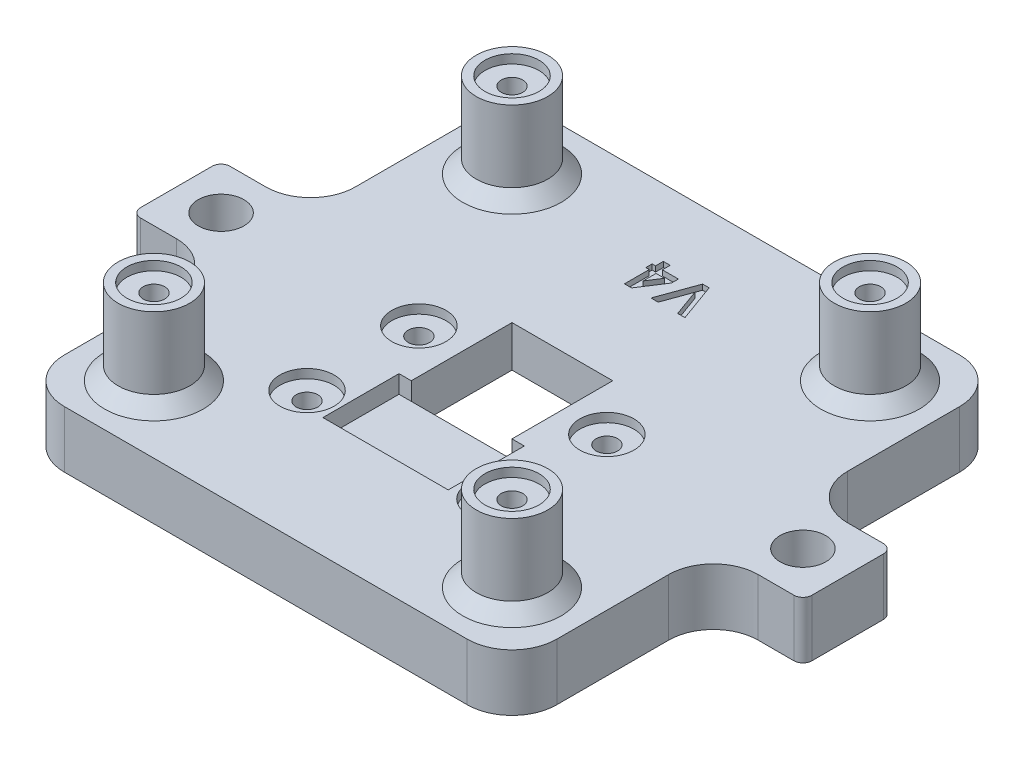
SolidWorks part; units mm, degrees
ref_plane "Front Plane" through (0, 0, 0) normal (0, 0, 1) x (1, 0, 0)
ref_plane "Top Plane" through (0, 0, 0) normal (0, 1, 0) x (1, 0, 0)
ref_plane "Right Plane" through (0, 0, 0) normal (1, 0, 0) x (0, 0, -1)
sketch "Sketch1" plane through (0, 0, 0) normal (0, 1, 0) x (1, 0, 0)
  line L1 (-27.5, 27.5) -> (27.5, 27.5)
  line L2 (-27.5, 27.5) -> (-27.5, -27.5)
  line L3 (-27.5, -27.5) -> (27.5, -27.5)
  line L4 (27.5, 27.5) -> (27.5, -27.5)
  line L5 (-27.5, 27.5) -> (27.5, -27.5) construction
  line L6 (-27.5, -27.5) -> (27.5, 27.5) construction
  point P0 (0, 0)
  dimension "D1" = 55
  dimension "D2" = 55
extrude "Boss-Extrude1" add sketch "Sketch1" along normal blind 6.35
sketch "Sketch2" plane through (0, 6.35, 0) normal (0, 1, 0) x (1, 0, 0)
  line L1 (-5.625, -5.625) -> (5.625, -5.625)
  line L2 (-5.625, -5.625) -> (-5.625, 5.625)
  line L3 (-5.625, 5.625) -> (5.625, 5.625)
  line L4 (5.625, -5.625) -> (5.625, 5.625)
  line L5 (-5.625, -5.625) -> (5.625, 5.625) construction
  line L6 (-5.625, 5.625) -> (5.625, -5.625) construction
  point P0 (0, 0)
  dimension "D1" = 11.25
extrude "Cut-Extrude1" cut sketch "Sketch2" against normal through all
sketch "Sketch3" plane through (0, 6.35, 0) normal (0, 1, 0) x (1, 0, 0)
  line L0 (0, 0) -> (0, 2.7158) construction
  line L1 (-7, -5.625) -> (7, -5.625)
  line L2 (-7, -5.625) -> (-7, -14.125)
  line L3 (-7, -14.125) -> (7, -14.125)
  line L4 (7, -5.625) -> (7, -14.125)
  line L6 (-5.625, -5.625) -> (5.625, -5.625) construction
  point P5 (0, -5.625)
  dimension "D1" = 14
  dimension "D2" = 8.5
extrude "Cut-Extrude2" cut sketch "Sketch3" against normal blind 2
sketch "Sketch4" plane through (0, 0, 0) normal (0, 1, 0) x (1, 0, 0)
  line L0 (0, 0) -> (0, 9.1234) construction
  line L2 (-12.5, 9.462) -> (12.5, 9.462) construction
  line L3 (-12.5, 9.462) -> (-12.5, -14.4) construction
  line L4 (-12.5, -14.4) -> (12.5, -14.4) construction
  line L5 (12.5, 9.462) -> (12.5, -14.4) construction
  point P7 (0, 9.462)
  point P8 (10.5, -12.4)
  point P9 (-10.5, -12.4)
  point P10 (-10.5, 0.1)
  point P11 (10.5, 0.1)
  dimension "D1" = 14.4
  dimension "D2" = 23.862
  dimension "D3" = 25
  dimension "D4" = 2
  dimension "D5" = 2
  dimension "D6" = 14.5
hole_wizard "CBORE for M2 SHCS2" positions "Sketch4" profile "Sketch15" counterbore size "M2" standard "ANSI Metric" end condition up to next
sketch "Sketch15" plane through (10.5, 0, -0.1) normal (1, 0, 0) x (0, 0, -1)
  line L0 (0, 0) -> (0, 6.35)
  line L1 (0, 6.35) -> (1.2, 6.35)
  line L3 (1.2, 6.35) -> (1.2, 2)
  line L4 (1.2, 2) -> (2.2, 2)
  line L5 (2.2, 2) -> (2.2, 0)
  line L7 (2.2, 0) -> (0, 0)
  line L11 (0, -6.35) -> (0, 107.95) construction
  dimension "Thru Hole Dia." = 2.4
  dimension "Thru Hole Depth" = 6.35
  dimension "C'Bore Dia." = 4.4
  dimension "C'Bore Depth" = 2
sketch "Sketch6" plane through (0, 6.35, 0) normal (0, 1, 0) x (1, 0, 0)
  line L1 (-20, -20) -> (20, -20) construction
  line L2 (-20, -20) -> (-20, 20) construction
  line L3 (-20, 20) -> (20, 20) construction
  line L4 (20, -20) -> (20, 20) construction
  line L5 (-20, -20) -> (20, 20) construction
  line L6 (-20, 20) -> (20, -20) construction
  circle A0 centre (-20, 20) radius 4
  circle A1 centre (20, 20) radius 4
  circle A2 centre (20, -20) radius 4
  circle A3 centre (-20, -20) radius 4
  point P0 (0, 0)
  dimension "D2" = 8
  dimension "D1" = 40
extrude "Boss-Extrude2" add sketch "Sketch6" along normal blind 9.5
sketch "Sketch10" plane through (0, 0, 0) normal (0, -1, 0) x (1, 0, 0)
  circle A0 centre (20, 20) radius 4 construction
  circle A1 centre (20, -20) radius 4 construction
  circle A2 centre (-20, -20) radius 4 construction
  circle A3 centre (-20, 20) radius 4 construction
  circle A4 centre (20, 20) radius 4 construction
  circle A5 centre (20, -20) radius 4 construction
  circle A6 centre (-20, -20) radius 4 construction
  circle A7 centre (-20, 20) radius 4 construction
  point P13 (-20, 20)
  point P14 (20, 20)
  point P15 (20, -20)
  point P16 (-20, -20)
hole_wizard "CBORE for M2 SHCS1" positions "Sketch10" profile "Sketch11" counterbore size "M2" standard "ANSI Metric" end condition through all
sketch "Sketch11" plane through (-20, 0, -20) normal (1, 0, 0) x (0, 0, -1)
  line L0 (0, 0) -> (0, 15.85)
  line L1 (0, 15.85) -> (1.2, 15.85)
  line L3 (1.2, 15.85) -> (1.2, 2)
  line L4 (1.2, 2) -> (2.2, 2)
  line L5 (2.2, 2) -> (2.2, 0)
  line L7 (2.2, 0) -> (0, 0)
  line L11 (0, -6.35) -> (0, 107.95) construction
  dimension "Thru Hole Dia." = 2.4
  dimension "Thru Hole Depth" = 15.85
  dimension "C'Bore Dia." = 4.4
  dimension "C'Bore Depth" = 2
sketch "Sketch12" plane through (0, 0, 0) normal (0, 0, 1) x (1, 0, 0)
  line L0 (27.5, 6.35) -> (27.5, 0) construction
  line L1 (-27.5, 6.35) -> (27.5, 6.35)
  line L2 (-27.5, 6.35) -> (-27.5, 15.85)
  line L3 (-27.5, 15.85) -> (27.5, 15.85)
  line L4 (27.5, 6.35) -> (27.5, 15.85)
  line L5 (-16, 15.85) -> (-24, 15.85) construction
extrude "Cut-Extrude3" [suppressed] cut sketch "Sketch12" against normal through all and the other way through all
sketch "Sketch13" plane through (0, 6.35, 0) normal (0, 1, 0) x (1, 0, 0)
  line L0 (0, 0) -> (0, -5.9289) construction
  circle A0 centre (-10.5, -12.4) radius 3.025
  circle A1 centre (-10.5, 0.1) radius 3.025
  circle A2 centre (10.5, -12.4) radius 3.025
  circle A3 centre (10.5, 0.1) radius 3.025
  circle A5 centre (-10.5, -12.4) radius 1.2 construction
  circle A6 centre (-10.5, 0.1) radius 1.2 construction
  dimension "D1" = 6.05
extrude "Cut-Extrude4" cut sketch "Sketch13" against normal blind 1
chamfer "Chamfer1" distance 1.75 angle 45 4 edges at (0, 0, -5.625) (5.625, 0, 0) (-5.625, 0, 0) (0, 0, 5.625)
sketch "Sketch14" plane through (0, 6.35, 0) normal (0, 1, 0) x (1, 0, 0)
  circle A0 centre (0, 0) radius 5.2973
sketch "Sketch16" plane through (0, 0, 0) normal (0, -1, 0) x (1, 0, 0)
  line L0 (0, 0) -> (30.2977, 0) construction
  line L1 (27.5, 27.5) -> (27.5, -27.5) construction
  line L2 (27.5, -5) -> (37.5, -5)
  line L3 (27.5, -5) -> (27.5, 5)
  line L4 (27.5, 5) -> (37.5, 5)
  line L5 (37.5, -5) -> (37.5, 5)
  line L6 (0, 0) -> (0, -32.0424) construction
  line L7 (-27.5, 5) -> (-37.5, 5)
  line L8 (-37.5, -5) -> (-37.5, 5)
  line L9 (-27.5, -5) -> (-37.5, -5)
  line L10 (-27.5, -5) -> (-27.5, 5)
  point P9 (27.5, 0)
  dimension "D1" = 10
  dimension "D2" = 10
extrude "Boss-Extrude3" add sketch "Sketch16" against normal up to surface (6.35 mm away) up to face at (-10.5, 6.35, 2.925)
sketch "Sketch17" plane through (0, 0, 0) normal (0, -1, 0) x (1, 0, 0)
  line L0 (37.5, 0) -> (27.5, 0) construction
  line L1 (37.5, -5) -> (37.5, 5) construction
  line L2 (27.5, -5) -> (27.5, -27.5) construction
  line L3 (0, 0) -> (0, -11.6553) construction
  circle A0 centre (32.5, 0) radius 2.55
  circle A1 centre (-32.5, 0) radius 2.55
  point P8 (32.5, 0)
  point P10 (-32.5, 0)
  point P17 (35.05, 0)
  dimension "D1" = 5.1
extrude "Cut-Extrude6" cut sketch "Sketch17" against normal through all
fillet "Fillet1" radius 5 8 edges at (27.5, 3.175, 5) (27.5, 3.175, -5) (-27.5, 3.175, 5) (-27.5, 3.175, -5) (-27.5, 3.175, -27.5) (-27.5, 3.175, 27.5) (27.5, 3.175, 27.5) (27.5, 3.175, -27.5)
fillet "Fillet2" radius 1 4 edges at (-37.5, 3.175, -5) (-37.5, 3.175, 5) (37.5, 3.175, 5) (37.5, 3.175, -5)
sketch "Sketch18" plane through (0, 15.85, 0) normal (0, 1, 0) x (1, 0, 0)
  circle A0 centre (-20, 20) radius 3.025
  circle A1 centre (-20, -20) radius 3.025
  circle A2 centre (20, 20) radius 3.025
  circle A3 centre (20, -20) radius 3.025
  dimension "D1" = 6.05
extrude "Cut-Extrude7" cut sketch "Sketch18" against normal blind 1
sketch "Sketch19" plane through (0, 6.35, 0) normal (0, 1, 0) x (1, 0, 0)
  line L0 (-16, 20) -> (16, 20) construction
  circle A0 centre (-20, 20) radius 4 construction
  circle A1 centre (-20, 20) radius 4 construction
  circle A2 centre (20, 20) radius 4 construction
  text T0 "V4" font "Century Gothic" height in points 16
extrude "Cut-Extrude8" cut sketch "Sketch19" against normal blind 0.6
chamfer "Chamfer2" distance 1.5 angle 45 4 edges at (-20, 6.35, -16) (20, 6.35, -16) (20, 6.35, 24) (-20, 6.35, 24)
equation "\"D2@Sketch1\"=\"D1@Sketch1\""
